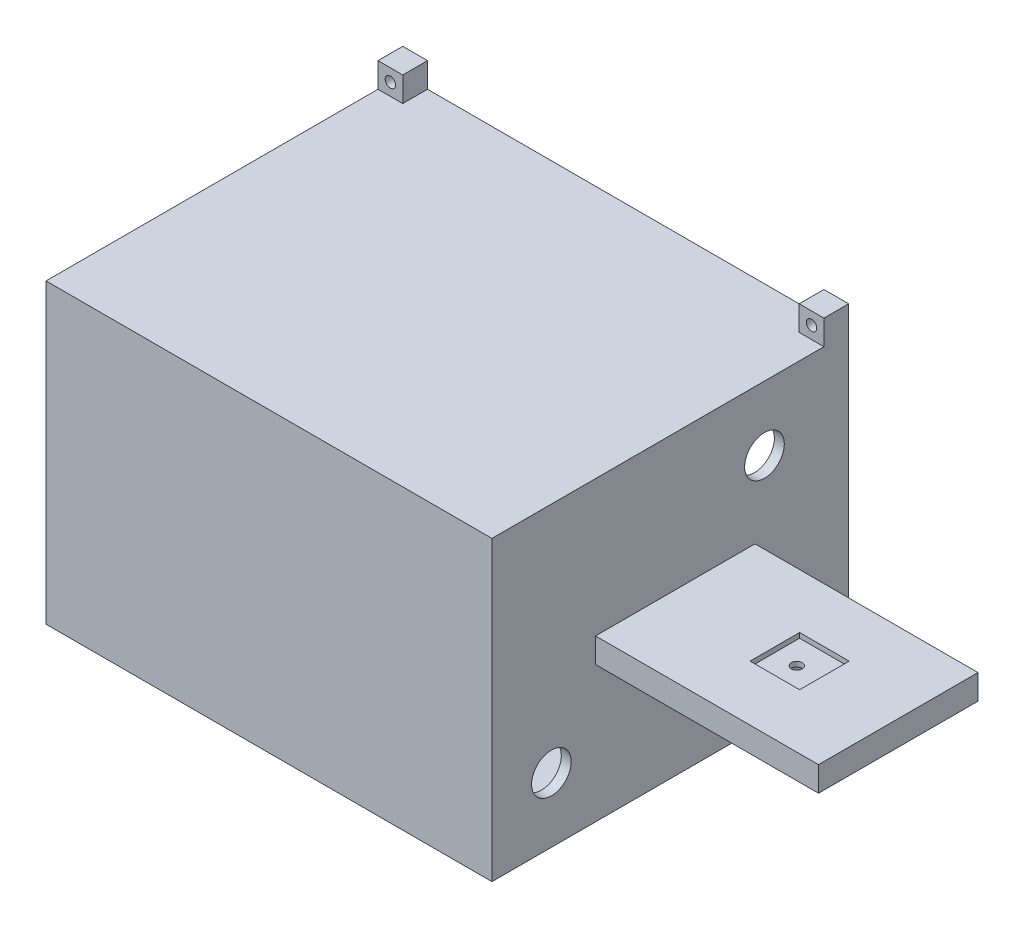
SolidWorks part; units mm, degrees
ref_plane "前基準面" through (0, 0, 0) normal (0, 0, 1) x (1, 0, 0)
ref_plane "上基準面" through (0, 0, 0) normal (0, 1, 0) x (1, 0, 0)
ref_plane "右基準面" through (0, 0, 0) normal (1, 0, 0) x (0, 0, -1)
sketch "草圖1" plane through (0, 0, 0) normal (0, 0, 1) x (1, 0, 0)
  line L0 (-75.5089, 25.5899) -> (59.4911, 25.5899)
  line L4 (-75.5089, -4.4101) -> (59.4911, -4.4101) construction
  line L5 (-75.5089, 25.5899) -> (-75.5089, -34.4101)
  line L6 (59.4911, 25.5899) -> (59.4911, -34.4101)
  line L7 (-75.5089, -34.4101) -> (59.4911, -34.4101)
  dimension "D1" = 135
  dimension "D2" = 60
extrude "填料-伸長1" add sketch "草圖1" along normal blind 70
sketch "草圖5" plane through (0, -34.4101, 0) normal (0, -1, 0) x (1, 0, 0)
  line L0 (14.4911, 70) -> (14.4911, 0)
  line L1 (-75.5089, 70) -> (59.4911, 70) construction
  line L2 (-75.5089, 0) -> (59.4911, 0) construction
  line L3 (14.4911, 0) -> (59.4911, 0)
  line L4 (59.4911, 0) -> (59.4911, 70)
  line L5 (59.4911, 70) -> (14.4911, 70)
  dimension "D1" = 45
sketch "草圖6" plane through (0, 25.5899, 0) normal (0, 1, 0) x (1, 0, 0)
  line L0 (14.4911, 0) -> (14.4911, -70)
  line L1 (14.4911, -70) -> (59.4911, -70)
  line L2 (59.4911, -70) -> (59.4911, 0)
  line L3 (59.4911, 0) -> (14.4911, 0)
extrude "除料-伸長1" cut sketch "草圖6" against normal blind 27.5
extrude "除料-伸長2" cut sketch "草圖5" against normal blind 27.5
sketch "草圖7" plane through (0, 0, 0) normal (0, 0, 1) x (1, 0, 0)
  line L0 (-75.5089, -34.4101) -> (14.4911, -34.4101) construction
  line L1 (-75.5089, 25.5899) -> (-75.5089, -34.4101) construction
  line L3 (-70.5089, -29.4101) -> (-70.5089, 20.5899)
  line L4 (-70.5089, 20.5899) -> (9.4911, 20.5899)
  line L5 (9.4911, 20.5899) -> (9.4911, -29.4101)
  line L6 (-70.5089, -29.4101) -> (9.4911, -29.4101)
  line L7 (14.4911, 25.5899) -> (-75.5089, 25.5899) construction
  line L8 (14.4911, -6.9101) -> (14.4911, -34.4101) construction
  point P11 (9.4911, -4.4101)
  point P12 (-70.5089, -4.4101)
  dimension "D1" = 5
  dimension "D2" = 5
  dimension "D3" = 5
  dimension "D4" = 5
  dimension "D5" = 80
  dimension "D6" = 50
extrude "除料-伸長3" cut sketch "草圖7" along normal blind 75
sketch "草圖8" plane through (0, 0, 0) normal (0, 0, -1) x (-1, 0, 0)
  line L2 (75.5089, 25.5899) -> (75.5089, -34.4101) construction
  line L3 (-13.4911, 24.5899) -> (-13.4911, -33.4101)
  line L4 (-13.4911, 24.5899) -> (74.5089, 24.5899)
  line L5 (74.5089, 24.5899) -> (74.5089, -33.4101)
  line L7 (71.5089, -30.4101) -> (71.5089, 21.5899)
  line L8 (71.5089, 21.5899) -> (-10.4911, 21.5899)
  line L9 (-10.4911, 21.5899) -> (-10.4911, -30.4101)
  line L11 (-14.4911, 25.5899) -> (75.5089, 25.5899) construction
  line L12 (-14.4911, -1.9101) -> (-14.4911, 25.5899) construction
  line L13 (71.5089, -30.4101) -> (-10.4911, -30.4101)
  line L14 (-13.4911, -33.4101) -> (74.5089, -33.4101)
  line L15 (75.5089, -34.4101) -> (-14.4911, -34.4101) construction
  dimension "D1" = 3
  dimension "D2" = 3
  dimension "D3" = 3
  dimension "D4" = 1
  dimension "D5" = 1
  dimension "D6" = 1
  dimension "D7" = 3
  dimension "D8" = 1
extrude "除料-伸長4" cut sketch "草圖8" against normal blind 6
ref_plane "平面1" through (14.4911, 0, 0) normal (1, 0, 0) x (0, 0, -1)
ref_plane "平面2" through (0, -34.4101, 0) normal (0, -1, 0) x (-1, 0, 0)
sketch "草圖10" plane through (0, -34.4101, 0) normal (0, -1, 0) x (-1, 0, 0)
  line L0 (75.5089, 0) -> (-14.4911, 0) construction
  line L1 (14.0089, -12) -> (35.5089, -12)
  line L2 (14.0089, -12) -> (14.0089, -27)
  line L3 (14.0089, -27) -> (35.5089, -27)
  line L4 (35.5089, -12) -> (35.5089, -27)
  line L5 (75.5089, -70) -> (75.5089, 0) construction
  point P6 (24.7589, -12)
  dimension "D1" = 21.5
  dimension "D2" = 15
  dimension "D3" = 12
  dimension "D4" = 40
extrude "除料-伸長6" cut sketch "草圖10" against normal blind 10
sketch "草圖12" plane through (14.4911, 0, 0) normal (1, 0, 0) x (0, 0, -1)
  line L0 (-35, 25.5899) -> (-35, -34.4101) construction
  line L1 (0, 25.5899) -> (-70, 25.5899) construction
  line L2 (-70, -34.4101) -> (0, -34.4101) construction
  line L5 (-51.0938, -9.4101) -> (-51.0938, 0.5899)
  line L7 (-70, -9.4101) -> (-51.0938, -9.4101)
  line L9 (-18.9062, 0.5899) -> (0, 0.5899)
  line L10 (0, 0.5899) -> (0, -9.4101)
  line L11 (0, -9.4101) -> (-18.9062, -9.4101)
  line L12 (-18.9062, -9.4101) -> (-18.9062, 0.5899)
  line L13 (-70, 0.5899) -> (-70, -9.4101)
  line L14 (-51.0938, 0.5899) -> (-70, 0.5899)
  dimension "D2" = 25
extrude "除料-伸長7" cut sketch "草圖12" along normal blind 45
ref_plane "平面3" through (0, -6.9101, 0) normal (0, -1, 0) x (-1, 0, 0)
sketch "草圖14" plane through (0, -6.9101, 0) normal (0, -1, 0) x (-1, 0, 0)
  line L4 (-59.4911, -35) -> (-70.9929, -35) construction
  line L5 (-59.4911, -18.9062) -> (-59.4911, -51.0938) construction
  line L6 (-38.1261, -30.0802) -> (-22.0179, -33)
  line L7 (-38.1261, -39.9198) -> (-22.0179, -37)
  line L8 (-39.0179, -40) -> (-39.0179, -45.1799) construction
  line L9 (-39.9097, -39.9198) -> (-56.0179, -37)
  line L10 (-39.9097, -30.0802) -> (-56.0179, -33)
  line L11 (-49.9929, -35) -> (-38.9929, -35) construction
  line L12 (-20.0179, -35) -> (-28.4331, -35) construction
  line L13 (-14.4911, -51.0938) -> (-14.4911, -18.9062) construction
  arc A2 (-39.9097, -39.9198) -> (-38.1261, -39.9198) centre (-39.0179, -35) ccw
  arc A3 (-22.0179, -37) -> (-22.0179, -33) centre (-22.0179, -35) ccw
  arc A5 (-56.0179, -37) -> (-56.0179, -33) centre (-56.0179, -35) cw
  arc A6 (-38.1261, -30.0802) -> (-39.9097, -30.0802) centre (-39.0179, -35) ccw
  point P21 (-58.0179, -35)
  point P22 (0, 0)
  dimension "D1" = 10
  dimension "D2" = 4
  dimension "D3" = 1.4732
  dimension "D4" = 5.5268
extrude "除料-伸長8" cut sketch "草圖14" against normal blind 3
ref_plane "平面4" through (0, -1.9101, 0) normal (0, 1, 0) x (1, 0, 0)
sketch "草圖15" plane through (0, -1.9101, 0) normal (0, 1, 0) x (1, 0, 0)
  line L0 (14.4911, -18.9062) -> (14.4911, -51.0938) construction
  line L1 (34.4911, -29.9062) -> (44.4911, -29.9062)
  line L2 (34.4911, -29.9062) -> (34.4911, -39.9062)
  line L3 (34.4911, -39.9062) -> (44.4911, -39.9062)
  line L4 (44.4911, -29.9062) -> (44.4911, -39.9062)
  line L5 (59.4911, -18.9062) -> (14.4911, -18.9062) construction
  dimension "D1" = 10
  dimension "D2" = 10
  dimension "D3" = 20
  dimension "D4" = 11
extrude "除料-伸長9" cut sketch "草圖15" against normal blind 1
sketch "草圖17" plane through (0, -6.9101, 0) normal (0, -1, 0) x (-1, 0, 0)
  line L0 (-58.0179, -35) -> (-20.0179, -35) construction
  line L1 (-39.0179, -40) -> (-39.0179, -30) construction
  arc A0 (-56.0179, -33) -> (-56.0179, -37) centre (-56.0179, -35) ccw construction
  arc A1 (-22.0179, -37) -> (-22.0179, -33) centre (-22.0179, -35) ccw construction
  arc A2 (-39.9097, -39.9198) -> (-38.1261, -39.9198) centre (-39.0179, -35) ccw construction
  arc A3 (-38.1261, -30.0802) -> (-39.9097, -30.0802) centre (-39.0179, -35) ccw construction
  circle A4 centre (-39.0179, -35) radius 1.0953
extrude "除料-伸長11" cut sketch "草圖17" against normal blind 7
sketch "草圖18" plane through (0, 0, 0) normal (0, 0, 1) x (1, 0, 0)
  line L0 (-75.5089, -4.4101) -> (9.4911, -4.4101) construction
  line L1 (14.4911, 25.5899) -> (9.4911, 25.5899)
  line L2 (14.4911, 25.5899) -> (14.4911, 30.5899)
  line L3 (14.4911, 25.5899) -> (-75.5089, 25.5899) construction
  line L4 (-30.5089, 25.5899) -> (-30.5089, -34.4101) construction
  line L5 (-38.5, -34.4101) -> (38.5, -34.4101) construction
  line L6 (14.4911, 30.5899) -> (9.4911, 30.5899)
  line L11 (9.4911, 25.5899) -> (9.4911, 30.5899)
  line L12 (-75.5089, 25.5899) -> (-70.5089, 25.5899)
  line L17 (-75.5089, -34.4101) -> (-70.5089, -34.4101)
  line L18 (-75.5089, -34.4101) -> (-75.5089, -39.4101)
  line L19 (-75.5089, -39.4101) -> (-70.5089, -39.4101)
  line L20 (-70.5089, -34.4101) -> (-70.5089, -39.4101)
  line L21 (14.4911, -34.4101) -> (9.4911, -34.4101)
  line L22 (9.4911, -34.4101) -> (9.4911, -39.4101)
  line L23 (14.4911, -39.4101) -> (9.4911, -39.4101)
  line L24 (14.4911, -34.4101) -> (14.4911, -39.4101)
  line L25 (-75.5089, 25.5899) -> (-75.5089, -34.4101) construction
  line L26 (9.4911, -29.4101) -> (9.4911, 20.5899) construction
  line L27 (-75.5089, 25.5899) -> (-75.5089, 30.5899)
  line L28 (-75.5089, 30.5899) -> (-70.5089, 30.5899)
  line L29 (-70.5089, 25.5899) -> (-70.5089, 30.5899)
  circle A2 centre (-73.0089, -36.9101) radius 1.05
  circle A3 centre (11.9911, -36.9101) radius 1.05
  circle A4 centre (11.9911, 28.0899) radius 1.05
  circle A5 centre (-73.0089, 28.0899) radius 1.05
  dimension "D3" = 2.1
  dimension "D1" = 2.1
  dimension "D2" = 2.1
  dimension "D4" = 2.1
extrude "填料-伸長2" add sketch "草圖18" along normal blind 5
ref_plane "平面5" through (0, 0, 70) normal (0, 0, 1) x (1, 0, 0)
sketch "草圖19" plane through (0, 0, 70) normal (0, 0, 1) x (1, 0, 0)
  line L0 (14.4911, -43.147) -> (14.4911, 43.147) construction
  line L1 (-75.5089, 25.5899) -> (14.4911, 25.5899)
  line L2 (-75.5089, 25.5899) -> (-75.5089, -34.4101)
  line L3 (-75.5089, -34.4101) -> (14.4911, -34.4101)
  line L4 (14.4911, 25.5899) -> (14.4911, -34.4101)
  dimension "D1" = 60
  dimension "D2" = 90
extrude "填料-伸長3" add sketch "草圖19" along normal blind 2
sketch "草圖20" plane through (14.4911, 0, 0) normal (1, 0, 0) x (0, 0, -1)
  line L0 (-72, -4.4101) -> (0, -4.4101) construction
  line L1 (-72, -34.4101) -> (-72, 25.5899) construction
  line L2 (0, -39.4101) -> (0, 30.5899) construction
  circle A0 centre (-60, -21.4101) radius 4
  circle A1 centre (-17, 12.5899) radius 4
  dimension "D1" = 8
  dimension "D2" = 8
  dimension "D3" = 17
  dimension "D4" = 17
  dimension "D5" = 17
  dimension "D6" = 12
extrude "除料-伸長12" cut sketch "草圖20" against normal blind 10
ref_plane "平面6" through (0, 0, 7) normal (0, 0, -1) x (-1, 0, 0)
sketch "草圖21" plane through (0, 0, 7) normal (0, 0, -1) x (-1, 0, 0)
  line L0 (-13.4911, -4.4101) -> (75.5089, -4.4101) construction
  line L1 (-13.4911, 24.5899) -> (-13.4911, -33.4101) construction
  line L2 (75.5089, 30.5899) -> (75.5089, -39.4101) construction
  line L3 (30.5089, 25.5899) -> (30.5089, -34.4101) construction
  line L4 (-9.4911, 25.5899) -> (70.5089, 25.5899) construction
  line L5 (-39.6, -34.4101) -> (39.6, -34.4101) construction
  line L6 (-14.4911, 43.147) -> (-14.4911, -43.147) construction
  line L7 (-12.4911, 23.5899) -> (73.5089, 23.5899)
  line L8 (-12.4911, 23.5899) -> (-12.4911, -32.4101)
  line L9 (-12.4911, -32.4101) -> (73.5089, -32.4101)
  line L10 (73.5089, 23.5899) -> (73.5089, -32.4101)
  point P18 (30.5089, -34.4101)
  dimension "D1" = 2
  dimension "D2" = 2
  dimension "D3" = 2
  dimension "D4" = 2
extrude "除料-伸長13" cut sketch "草圖21" against normal blind 63
